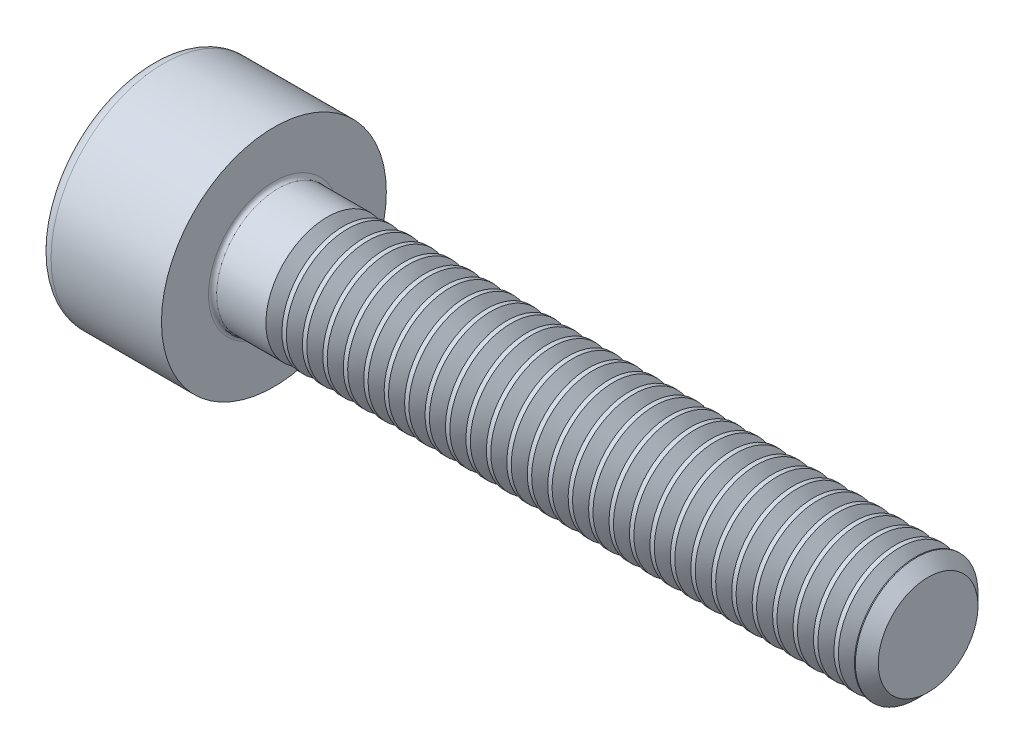
SolidWorks part; units mm, degrees
revolve "Base-Revolve" add sketch "BodySke"
sketch "BodySke" plane through (0, 0, 0) normal (0, 0, 1) x (1, 0, 0)
  line L0 (0, 0) -> (0, 2.75)
  line L1 (0, 2.75) -> (3, 2.75)
  line L2 (3, 2.75) -> (3, 1.5)
  line L3 (3, 1.5) -> (18.7195, 1.5)
  line L4 (19, 1.2195) -> (19, 0)
  line L5 (19, 0) -> (0, 0)
  line L6 (-31.75, 0) -> (127, 0) construction
  line L8 (19, 1.2195) -> (18.7195, 1.5)
  line L10 (19, -1.2195) -> (18.7195, -1.5) construction
  line L11 (3.5, 9.525) -> (3.5, 3.175) construction
  line L12 (3, 9.525) -> (3, 3.175) construction
  line L13 (3, 9.525) -> (3, 3.175) construction
cosmetic thread "ThreadCosmetic" [suppressed]
fillet "Fillet1" radius 0.1 1 edges at (3, 0, 1.5)
fillet "Fillet2" radius 0.3 1 edges at (0, 0, 2.75)
ref_plane "Plane1" through (0, 0, 0) normal (0, 0, 1) x (1, 0, 0)
ref_plane "Plane2" through (0, 0, 0) normal (0, 1, 0) x (1, 0, 0)
ref_plane "Plane3" through (0, 0, 0) normal (1, 0, 0) x (0, 0, -1)
sketch "Sketch2" plane through (0, 0, 0) normal (0, 0, 1) x (1, 0, 0)
  line L0 (0, 1.26) -> (1.3, 1.26)
  line L1 (1.3, 1.26) -> (2.0275, 0)
  line L2 (-31.75, 0) -> (127, 0) construction
  line L3 (2.0275, 0) -> (0, 0)
  line L4 (0, 0) -> (0, 1.26)
  line L6 (0, 0) -> (47.625, 0) construction
revolve "Hex-PreBroach" cut sketch "Sketch2" angle 360 about L6
sketch "Sketch3" plane through (0, 0, 0) normal (-1, 0, 0) x (0, 0.5, 0.866)
  line L0 (0.7275, 1.26) -> (-0.7275, 1.26)
  line L1 (-0.7275, 1.26) -> (-1.4549, 0)
  line L2 (0.7275, 1.26) -> (1.4549, 0)
  line L3 (0.7275, -1.26) -> (1.4549, 0)
  line L4 (0.7275, -1.26) -> (-0.7275, -1.26)
  line L5 (-0.7275, -1.26) -> (-1.4549, 0)
extrude "Hex" cut sketch "Sketch3" against normal blind 1.3
sketch "ThdSchSke" plane through (0, 0, 0) normal (0, 0, 1) x (1, 0, 0)
  line L0 (4.5, -1.2195) -> (4.3036, -1.5)
  line L1 (4.5, -1.2195) -> (4.6964, -1.5)
  line L2 (4.6964, -1.5) -> (4.6964, -1.875)
  line L3 (-3.175, 0) -> (5.1513, 0) construction
  line L4 (0, 2.45) -> (0, -2.45) construction
  line L5 (4.6964, -1.875) -> (4.3036, -1.875)
  line L6 (4.3036, -1.875) -> (4.3036, -1.5)
revolve "ThreadSchematic" cut sketch "ThdSchSke" angle 360 about L3
pattern_linear "ThdSchPat" count 29 spacing 0.5 along (1, 0, 0) of "ThreadSchematic"
equation "\"D2@Sketch3\" = \"Hex_size@Sketch3\" / 2"
equation "\"D1@Sketch3\" = \"Hex_size@Sketch3\" / 2"
equation "\"D1@Sketch2\" = \"Hex_size@Sketch3\" / 2"
equation "\"Thread_minor@ThreadCosmetic\"  =  \"Minor_dia@BodySke\""
equation "\"Depth@Sketch2\" =  \"Key_eng@Hex\""
equation "\"Thread_length@ThreadCosmetic\" = ((sgn( (\"Length@BodySke\" - \"Advance@BodySke\" * 3.0) - \"Thread_nom@BodySke\" )-1)*( (\"Length@BodySke\" - \"Advance@BodySke\" * 3.0) - \"Thread_nom@BodySke\" ))/-2+ \"Thread_nom@BodySke\""
equation "\"Thread_minor@ThdSchSke\" = \"Minor_dia@BodySke\""
equation "\"Diameter@ThdSchSke\" = \"Diameter@BodySke\""
equation "\"Overcut@ThdSchSke\" = \"Diameter@BodySke\" * 1.25"
equation "\"Start@ThdSchSke\" = \"Head_ht@BodySke\" + \"Length@BodySke\" - \"Thread_length@ThreadCosmetic\"  '---Non-countersunk---"
equation "\"Num_threads@ThdSchPat\" = int( \"Thread_length@ThreadCosmetic\" / \"Advance@BodySke\" + 0.999 )  + 1"
equation "\"Advance@ThdSchPat\" = \"Thread_length@ThreadCosmetic\" /  (\"Num_threads@ThdSchPat\" - 1) 'relax it"
equation "\"Num_threads@ThdSchPat\" = \"Num_threads@ThdSchPat\" - sgn( \"Num_threads@ThdSchPat\" - 1) '---chamfered tips only---"
